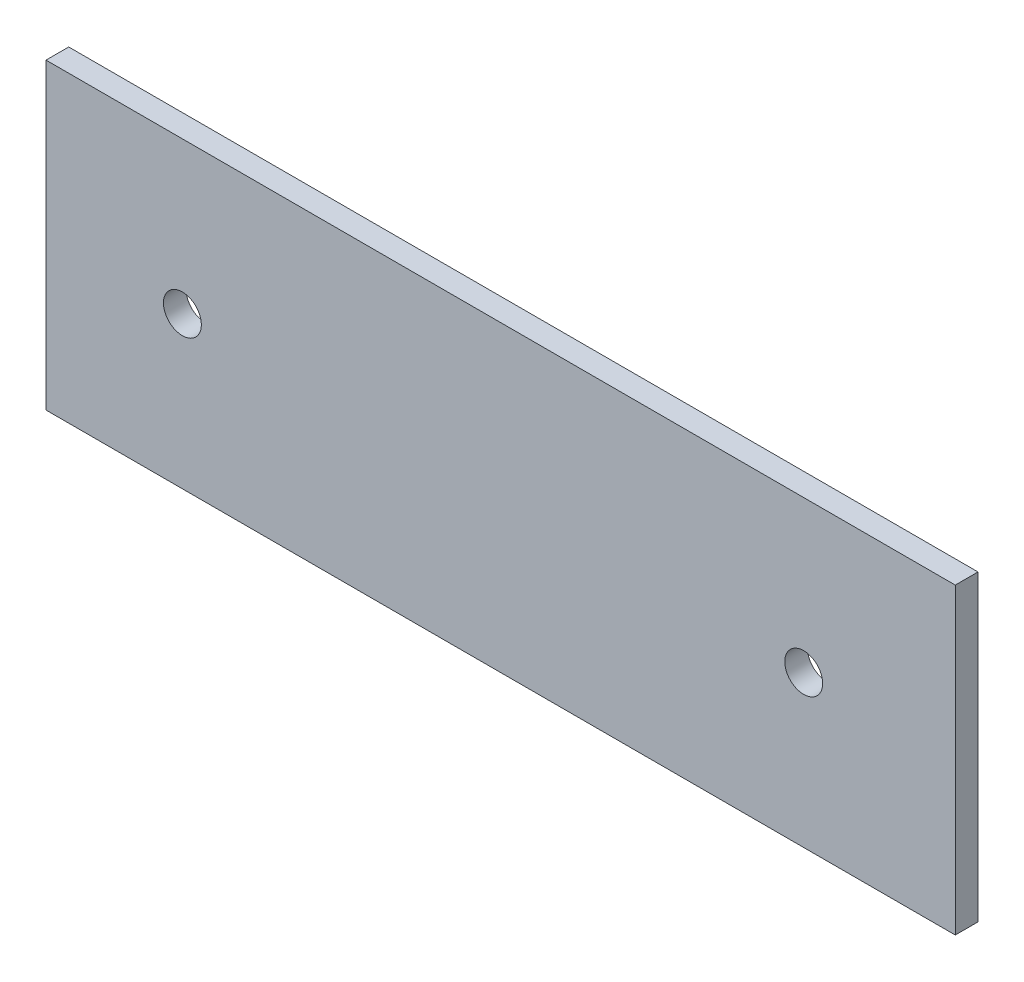
SolidWorks part; units mm, degrees
ref_plane "Piano frontale" through (0, 0, 0) normal (0, 0, 1) x (1, 0, 0)
ref_plane "Piano superiore" through (0, 0, 0) normal (0, 1, 0) x (1, 0, 0)
ref_plane "Piano destro" through (0, 0, 0) normal (1, 0, 0) x (0, 0, -1)
sketch "Schizzo1" plane through (0, 0, 0) normal (0, 0, 1) x (1, 0, 0)
  line L1 (0, 0) -> (120, 0)
  line L2 (0, 0) -> (0, -40)
  line L3 (0, -40) -> (120, -40)
  line L4 (120, 0) -> (120, -40)
  dimension "D1" = 120
  dimension "D2" = 40
extrude "Estrusione-Estrusione1" add sketch "Schizzo1" along normal blind 3
sketch "Schizzo2" plane through (0, 0, 3) normal (0, 0, 1) x (1, 0, 0)
  line L0 (0, 0) -> (0, -40) construction
  line L1 (120, 0) -> (0, 0) construction
  circle A0 centre (18, -20) radius 2.5
  dimension "D1" = 5
  dimension "D2" = 18
  dimension "D3" = 20
extrude "Taglio-Estrusione1" cut sketch "Schizzo2" against normal blind 3
sketch "Schizzo3" plane through (0, 0, 3) normal (0, 0, 1) x (1, 0, 0)
  line L0 (120, 0) -> (0, 0) construction
  line L1 (120, -40) -> (120, 0) construction
  circle A0 centre (100, -20) radius 2.5
  dimension "D1" = 5
  dimension "D2" = 20
  dimension "D3" = 20
extrude "Taglio-Estrusione2" cut sketch "Schizzo3" against normal blind 3
sketch "Schizzo4" plane through (0, 0, 3) normal (0, 0, 1) x (1, 0, 0)
  text T0 "18\r\n"
  text T1 "20\r\n"
